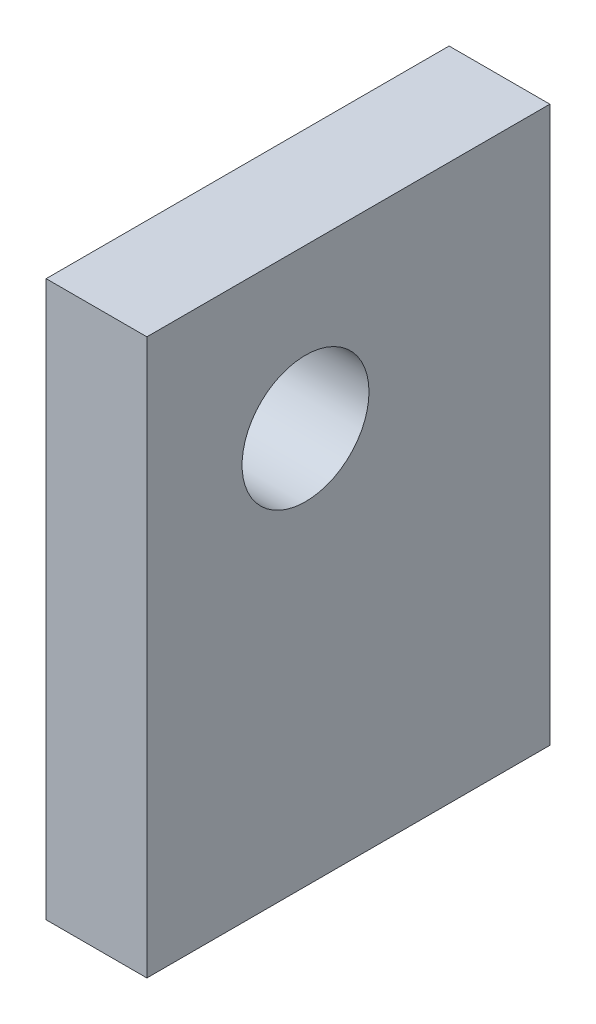
SolidWorks part; units mm, degrees
ref_plane "Front Plane" through (0, 0, 0) normal (0, 0, 1) x (1, 0, 0)
ref_plane "Top Plane" through (0, 0, 0) normal (0, 1, 0) x (1, 0, 0)
ref_plane "Right Plane" through (0, 0, 0) normal (1, 0, 0) x (0, 0, -1)
sketch "Sketch2" plane through (0, 0, 0) normal (0, 1, 0) x (1, 0, 0)
  line L1 (0, 0) -> (25.4, 0)
  line L2 (0, 0) -> (0, 101.6)
  line L3 (0, 101.6) -> (25.4, 101.6)
  line L4 (25.4, 0) -> (25.4, 101.6)
  dimension "D1" = 25.4
  dimension "D2" = 101.6
extrude "Boss-Extrude1" add sketch "Sketch2" along normal blind 140
sketch "Sketch4" plane through (25.4, 0, 0) normal (1, 0, 0) x (0, 0, -1)
  line L1 (0, 140) -> (40, 140)
  line L2 (0, 140) -> (0, 100)
  line L3 (0, 100) -> (40, 100)
  line L4 (40, 140) -> (40, 100)
  circle A0 centre (40, 100) radius 16
  dimension "D1" = 40
  dimension "D2" = 40
extrude "Cut-Extrude2" cut sketch "Sketch4" against normal blind 500 contours A0
